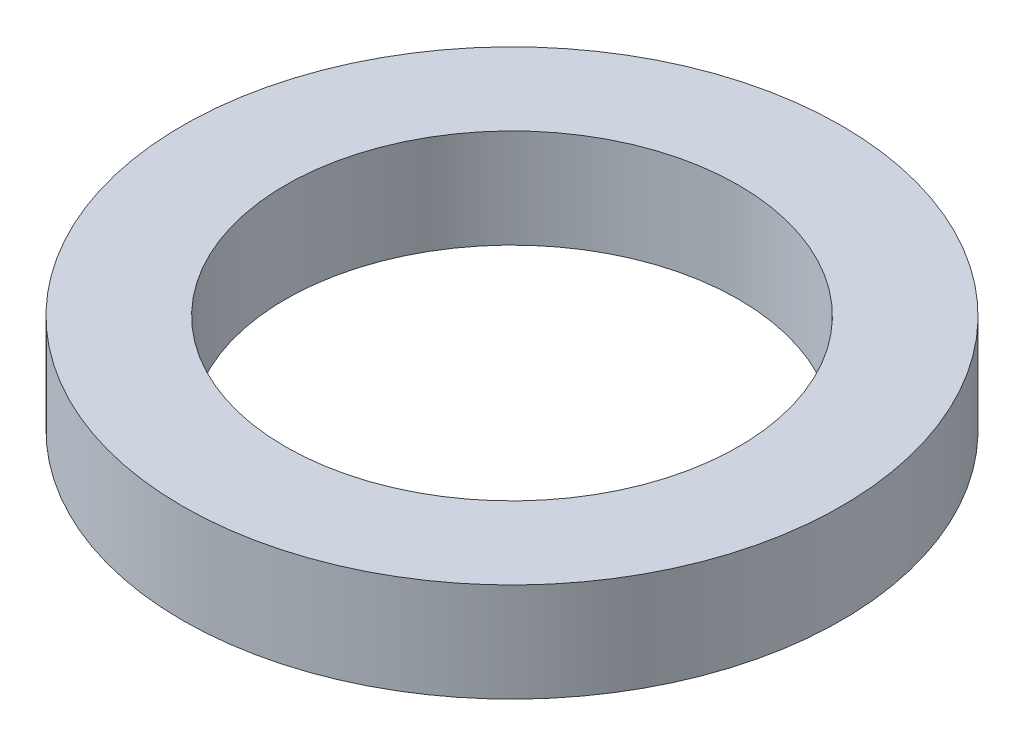
SolidWorks part; units mm, degrees
ref_plane "Front Plane" through (0, 0, 0) normal (0, 0, 1) x (1, 0, 0)
ref_plane "Top Plane" through (0, 0, 0) normal (0, 1, 0) x (1, 0, 0)
ref_plane "Right Plane" through (0, 0, 0) normal (1, 0, 0) x (0, 0, -1)
sketch "Sketch1" plane through (0, 0, 0) normal (0, 1, 0) x (1, 0, 0)
  circle A0 centre (0, 0) radius 4
  circle A1 centre (0, 0) radius 2.75
  dimension "D1" = 8
  dimension "D2" = 5.5
extrude "Boss-Extrude1" add sketch "Sketch1" along normal blind 1.2
